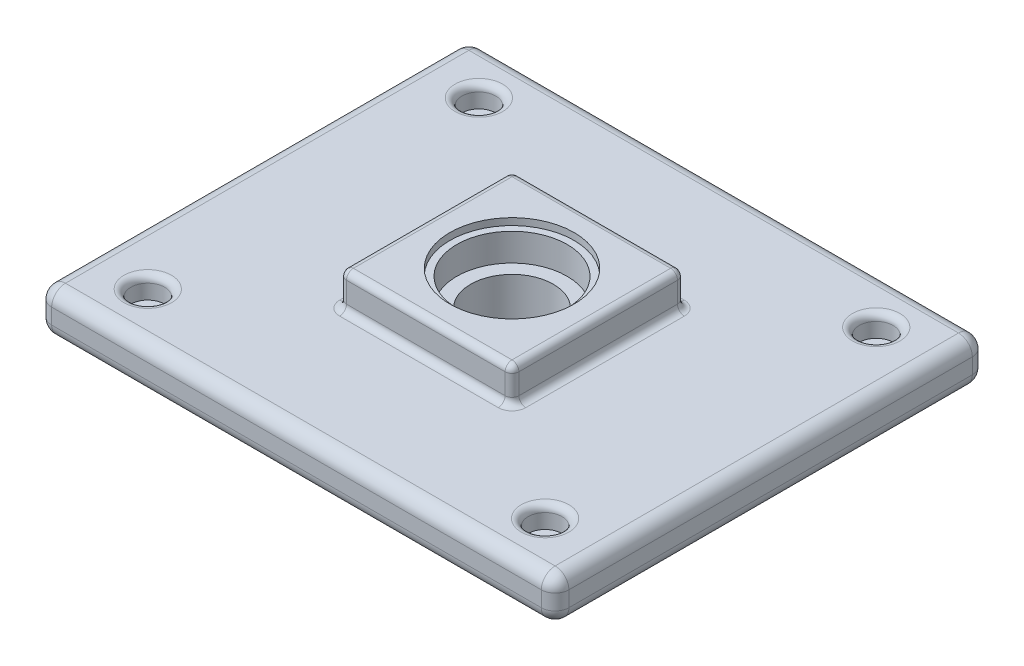
SolidWorks part; units mm, degrees
material "Epoxy, Unfilled"
ref_plane "Front Plane" through (0, 0, 0) normal (0, 0, 1) x (1, 0, 0)
ref_plane "Top Plane" through (0, 0, 0) normal (0, 1, 0) x (1, 0, 0)
ref_plane "Right Plane" through (0, 0, 0) normal (1, 0, 0) x (0, 0, -1)
sketch "Sketch1" plane through (0, 0, 0) normal (0, 1, 0) x (1, 0, 0)
  line L1 (300, 250) -> (-300, 250)
  line L2 (300, 250) -> (300, -250)
  line L3 (300, -250) -> (-300, -250)
  line L4 (-300, 250) -> (-300, -250)
  line L5 (300, 250) -> (-300, -250) construction
  line L6 (300, -250) -> (-300, 250) construction
  point P0 (0, 0)
  dimension "D1" = 600
  dimension "D2" = 500
extrude "Boss-Extrude1" add sketch "Sketch1" along normal blind 50
sketch "Sketch2" plane through (0, 50, 0) normal (0, 1, 0) x (1, 0, 0)
  circle A5 centre (-230.4664, -192.0553) radius 19.6
  circle A6 centre (230.4664, 192.0553) radius 19.6
  circle A7 centre (230.4664, -192.0553) radius 19.6
  circle A8 centre (-230.4664, 192.0553) radius 19.6
  point P0 (0, 0)
  point P5 (0, 0)
  point P8 (0, 0)
  point P13 (0, 0)
  dimension "D1" = 300
  dimension "D2" = 2
  dimension "D3" = 300
  dimension "D4" = 300
  dimension "D5" = 300
extrude "Cut-Extrude1" cut sketch "Sketch2" against normal blind 25
scale "Scale1" scale about centroid uniform scaling yes scale factor 0.125
fillet "Fillet4" radius 1 4 edges at (-28.8083, 28.0363, 26.4569) (28.8083, 28.0363, 21.5569) (28.8083, 28.0363, -21.5569) (-28.8083, 28.0363, -26.4569)
sketch "Sketch3" plane through (0, 21.7863, 0) normal (0, -1, 0) x (-1, 0, 0)
  line L1 (-12.5, -12.5) -> (12.5, -12.5)
  line L2 (-12.5, -12.5) -> (-12.5, 12.5)
  line L3 (-12.5, 12.5) -> (12.5, 12.5)
  line L4 (12.5, -12.5) -> (12.5, 12.5)
  line L5 (-12.5, -12.5) -> (12.5, 12.5) construction
  line L6 (-12.5, 12.5) -> (12.5, -12.5) construction
  point P0 (0, 0)
  dimension "D1" = 25
  dimension "D2" = 25
extrude "Boss-Extrude2" add sketch "Sketch3" along normal blind 5
sketch "Sketch4" plane through (0, 16.7863, 0) normal (0, -1, 0) x (1, 0, 0)
  circle A0 centre (0, 0) radius 9
extrude "Cut-Extrude2" cut sketch "Sketch4" against normal blind 1
sketch "Sketch5" plane through (0, 17.7863, 0) normal (0, -1, 0) x (-1, 0, 0)
  circle A0 centre (0, 0) radius 8
extrude "Cut-Extrude3" cut sketch "Sketch5" against normal blind 4
sketch "Sketch6" plane through (0, 21.7863, 0) normal (0, -1, 0) x (-1, 0, 0)
  circle A0 centre (0, 0) radius 6
extrude "Cut-Extrude4" cut sketch "Sketch6" against normal through all
ref_plane "Plane3" through (0, 24.9113, 0) normal (0, 1, 0) x (1, 0, 0)
mirror "Mirror1" about plane through (0, 24.9113, 0) normal (0, 1, 0) of "Boss-Extrude2", "Cut-Extrude2", "Cut-Extrude3"
fillet "Fillet6" radius 1 24 edges at (0, 16.7863, 12.5) (0, 21.7863, 12.5) (-12.5, 19.2863, 12.5) (-12.5, 16.7863, 0) (-12.5, 21.7863, 0) (12.5, 16.7863, 0) (12.5, 19.2863, 12.5) (12.5, 21.7863, 0) (-12.5, 19.2863, -12.5) (0, 16.7863, -12.5) (12.5, 19.2863, -12.5) (0, 21.7863, -12.5) (-12.5, 33.0363, 0) (-12.5, 28.0363, 0) (-12.5, 30.5363, 12.5) (0, 33.0363, 12.5) (0, 28.0363, 12.5) (12.5, 30.5363, 12.5) (12.5, 33.0363, 0) (12.5, 28.0363, 0) (12.5, 30.5363, -12.5) (0, 33.0363, -12.5) (-12.5, 30.5363, -12.5) (0, 28.0363, -12.5)
fillet "Fillet7" radius 2 12 edges at (-37.5, 28.0363, 0) (-37.5, 21.7863, 0) (-37.5, 24.9113, 31.25) (0, 28.0363, 31.25) (0, 21.7863, 31.25) (37.5, 24.9113, 31.25) (37.5, 28.0363, 0) (37.5, 21.7863, 0) (37.5, 24.9113, -31.25) (0, 28.0363, -31.25) (-37.5, 24.9113, -31.25) (0, 21.7863, -31.25)
